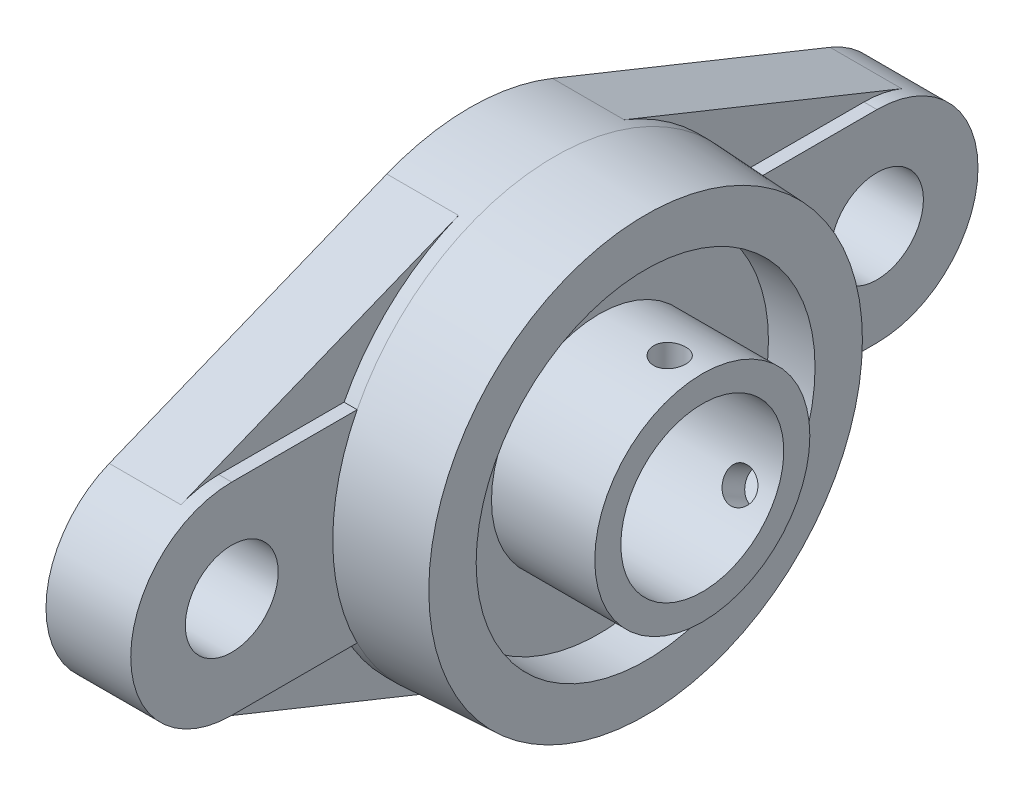
SolidWorks part; units mm, degrees
material "可锻铸铁"
ref_plane "前视基准面" through (0, 0, 0) normal (0, 0, 1) x (1, 0, 0)
ref_plane "上视基准面" through (0, 0, 0) normal (0, 1, 0) x (1, 0, 0)
ref_plane "右视基准面" through (0, 0, 0) normal (1, 0, 0) x (0, 0, -1)
ref_plane "基准面4" through (13, 0, 0) normal (1, 0, 0) x (0, 0, -1)
sketch "草图1" plane through (13, 0, 0) normal (1, 0, 0) x (0, 0, -1)
  line L0 (49.5, 15.5) -> (30.2614, 15.5)
  line L1 (-30.2614, 15.5) -> (-49.5, 15.5)
  line L2 (-49.5, -15.5) -> (-30.2614, -15.5)
  line L3 (30.2614, -15.5) -> (49.5, -15.5)
  arc A0 (30.2614, 15.5) -> (-30.2614, 15.5) centre (0, 0) ccw
  arc A1 (-49.5, 15.5) -> (-49.5, -15.5) centre (-49.5, 0) ccw
  arc A2 (-30.2614, -15.5) -> (30.2614, -15.5) centre (0, 0) ccw
  arc A3 (49.5, -15.5) -> (49.5, 15.5) centre (49.5, 0) ccw
extrude "凸台-拉伸1" add sketch "草图1" against normal blind 2
sketch "草图2" plane through (11, 0, 0) normal (-1, 0, 0) x (0, 0, 1)
  line L0 (12.7071, 31.5362) -> (55.2929, 14.3768)
  line L1 (55.2929, -14.3768) -> (12.7071, -31.5362)
  line L2 (-12.7071, -31.5362) -> (-55.2929, -14.3768)
  line L3 (-55.2929, 14.3768) -> (-12.7071, 31.5362)
  arc A0 (-12.7071, 31.5362) -> (12.7071, 31.5362) centre (0, 0) cw
  arc A1 (55.2929, 14.3768) -> (55.2929, -14.3768) centre (49.5, 0) cw
  arc A2 (12.7071, -31.5362) -> (-12.7071, -31.5362) centre (0, 0) cw
  arc A3 (-55.2929, -14.3768) -> (-55.2929, 14.3768) centre (-49.5, 0) cw
extrude "凸台-拉伸2" add sketch "草图2" along normal blind 11
sketch "草图3" plane through (13, 0, 0) normal (1, 0, 0) x (0, 0, -1)
  circle A0 centre (0, 0) radius 34
extrude "凸台-拉伸3" add sketch "草图3" along normal blind 14 draft 3
hole_wizard "M45 间隙孔1" positions "草图5" profile "草图4" hole size "M45" standard "ANSI Metric"
sketch "草图5" plane through (27, 0, 0) normal (1, 0, 0) x (0, 0, -1)
  point P0 (0, 0)
sketch "草图4" plane through (27, 0, 0) normal (0, 1, 0) x (0, 0, -1)
  line L0 (0, 0) -> (0, 7.15)
  line L1 (0, 7.15) -> (26, 7.15)
  line L2 (26, 7.15) -> (26, 0)
  line L5 (26, 0) -> (0, 0)
  line L10 (0, 7.15) -> (-26, 7.15) construction
  line L11 (0, -6.35) -> (0, 107.95) construction
  dimension "孔直径" = 52
  dimension "孔深度" = 7.15
  dimension "导头角度" = 180
ref_plane "基准面5" through (0, 0, 0) normal (0, 0, -1) x (-1, 0, 0)
sketch "草图6" plane through (0, 0, 0) normal (0, 0, -1) x (-1, 0, 0)
  line L0 (-35.7, 16.5) -> (-35.7, 0)
  line L1 (-35.7, 0) -> (-19.85, 0)
  line L2 (-19.85, 0) -> (-19.85, 16.5)
  line L3 (-19.85, 16.5) -> (-35.7, 16.5)
  line L4 (-35.7, 0) -> (-19.85, 0) construction
revolve "旋转1" add sketch "草图6" angle 360 about L4
hole_wizard "Ø14.25 (14.25) 直径孔1" positions "草图8" profile "草图7" hole size "Ø14.25" standard "ANSI Metric" end condition through all
sketch "草图8" plane through (13, 0, 0) normal (1, 0, 0) x (0, 0, -1)
  point P0 (-49.5, 0)
  point P1 (49.5, 0)
sketch "草图7" plane through (13, 0, 49.5) normal (0, 1, 0) x (0, 0, -1)
  line L0 (0, 0) -> (0, 13)
  line L1 (0, 13) -> (7.125, 13)
  line L2 (7.125, 13) -> (7.125, 0)
  line L5 (7.125, 0) -> (0, 0)
  line L11 (0, -6.35) -> (0, 107.95) construction
  dimension "通孔孔直径" = 14.25
  dimension "通孔孔深度" = 13
hole_wizard "M24 六角头螺栓的柱形沉头孔1" positions "草图10" profile "草图9" counterbore size "M24" standard "ANSI Metric"
sketch "草图10" plane through (0, 0, 0) normal (-1, 0, 0) x (0, 0, 1)
  point P0 (0, 0)
sketch "草图9" plane through (0, 0, 0) normal (0, 1, 0) x (0, 0, 1)
  line L0 (0, 0) -> (0, 35.7)
  line L1 (0, 35.7) -> (12.5, 35.7)
  line L3 (12.5, 35.7) -> (12.5, 2)
  line L4 (12.5, 2) -> (26, 2)
  line L5 (26, 2) -> (26, 0)
  line L7 (26, 0) -> (0, 0)
  line L11 (0, -6.35) -> (0, 107.95) construction
  dimension "通孔孔直径" = 25
  dimension "通孔孔深度" = 35.7
  dimension "柱形沉头孔直径" = 52
  dimension "柱形沉头孔深度" = 2
ref_plane "基准面6" through (0, -6.1279, -10.6139) normal (0, 0.5, 0.866) x (1, 0, 0)
hole_wizard "孔1" positions "草图12" profile "草图11" legacy
sketch "草图12" plane through (0, -6.1279, -10.6139) normal (0, 0.5, 0.866) x (1, 0, 0)
  point P0 (30.7, 0)
sketch "草图11" plane through (30.7, -6.1279, -10.6139) normal (1, 0, 0) x (0, -0.866, 0.5)
  line L0 (0, 0) -> (0, 61.0358)
  line L1 (0, 61.0358) -> (2.4585, 61.0358)
  line L2 (2.4585, 61.0358) -> (2.4585, 0)
  line L3 (2.4585, 0) -> (0, 0)
  line L4 (0, 110) -> (0, -10) construction
  dimension "直径" = 4.917
  dimension "深度" = 61.0358
ref_plane "基准面7" through (0, 12.2558, 0) normal (0, -1, 0) x (-1, 0, 0)
hole_wizard "孔2" positions "草图14" profile "草图13" legacy
sketch "草图14" plane through (0, 12.2558, 0) normal (0, -1, 0) x (-1, 0, 0)
  point P0 (-30.7, 0)
sketch "草图13" plane through (30.7, 12.2558, 0) normal (1, 0, 0) x (0, 0, -1)
  line L0 (0, 0) -> (0, 21.7442)
  line L1 (0, 21.7442) -> (2.4585, 21.7442)
  line L2 (2.4585, 21.7442) -> (2.4585, 0)
  line L3 (2.4585, 0) -> (0, 0)
  line L4 (0, 110) -> (0, -10) construction
  dimension "直径" = 4.917
  dimension "深度" = 21.7442
